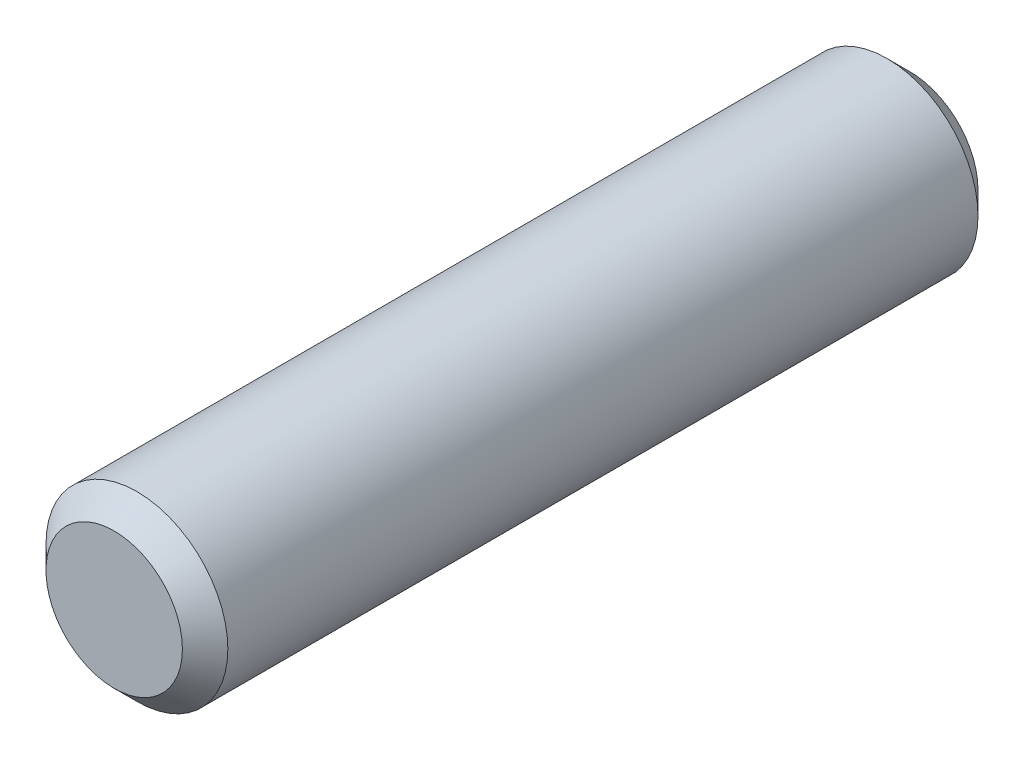
SolidWorks part; units mm, degrees
ref_plane "Plan1" through (0, 0, 0) normal (0, 0, 1) x (1, 0, 0)
ref_plane "Plan2" through (0, 0, 0) normal (0, 1, 0) x (1, 0, 0)
ref_plane "Plan3" through (0, 0, 0) normal (1, 0, 0) x (0, 0, -1)
sketch "Esquisse1" plane through (0, 0, 0) normal (0, 0, 1) x (1, 0, 0)
  circle A0 centre (0, 0) radius 4
  dimension "D1" = 8
extrude "Base-Extrusion" add sketch "Esquisse1" along normal blind 35
chamfer "Chanfrein1" distance 1 angle 45
